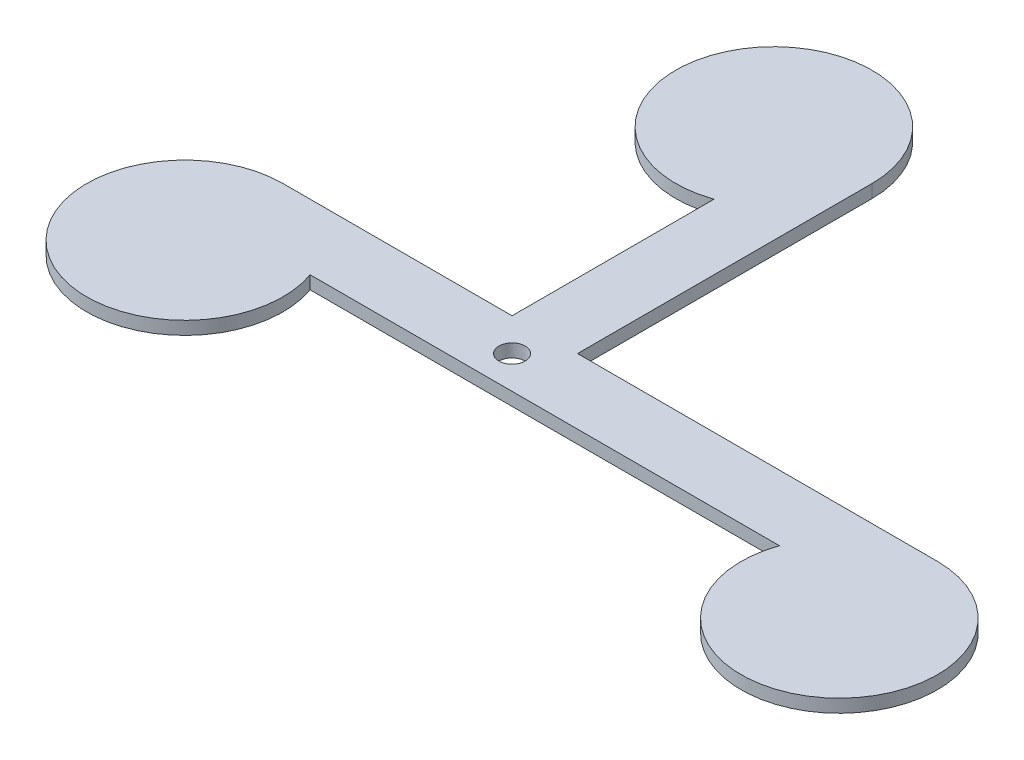
SolidWorks part; units mm, degrees
ref_plane "Front Plane" through (0, 0, 0) normal (0, 0, 1) x (1, 0, 0)
ref_plane "Top Plane" through (0, 0, 0) normal (0, 1, 0) x (1, 0, 0)
ref_plane "Right Plane" through (0, 0, 0) normal (1, 0, 0) x (0, 0, -1)
sketch "BaseSketch" plane through (0, 0, 0) normal (0, 1, 0) x (1, 0, 0)
  line L2 (35, 15) -> (0, 15)
  line L3 (35, 15) -> (35, 45.8579)
  line L4 (45, 15) -> (45, 60)
  line L5 (45, 5) -> (14.1421, 5)
  line L6 (45, 5) -> (85.8579, 5)
  line L7 (45, 15) -> (100, 15)
  arc A0 (0, 15) -> (14.1421, 5) centre (0, 0) ccw
  arc A1 (45, 60) -> (35, 45.8579) centre (30, 60) ccw
  arc A2 (85.8579, 5) -> (100, 15) centre (100, 0) ccw
  dimension "D3" = 15
  dimension "D6" = 15
  dimension "D7" = 15
  dimension "D1" = 10
  dimension "D2" = 10
  dimension "D4" = 45
  dimension "D5" = 55
extrude "BaseExtrude" add sketch "BaseSketch" along normal blind 2 contours A1 L3 L2 A0 L5 L6 A2 L7 L4
sketch "Sketch1" plane through (0, 0, 0) normal (0, -1, 0) x (1, 0, 0)
  line L0 (14.1421, -5) -> (85.8579, -5) construction
  circle A0 centre (40, -10) radius 2
  dimension "D1" = 5
  dimension "D2" = 4
extrude "Cut-Extrude1" cut sketch "Sketch1" against normal through all
sketch "Sketch2" plane through (0, 0, 0) normal (0, -1, 0) x (1, 0, 0)
  circle A1 centre (40, -10) radius 2 construction
  circle A2 centre (40, -16.5) radius 2.45
  dimension "D2" = 6.5
extrude "Boss-Extrude1" add sketch "Sketch2" along normal blind 2
fillet "Fillet1" radius 1 1 edges at (40, -2, -18.95)
